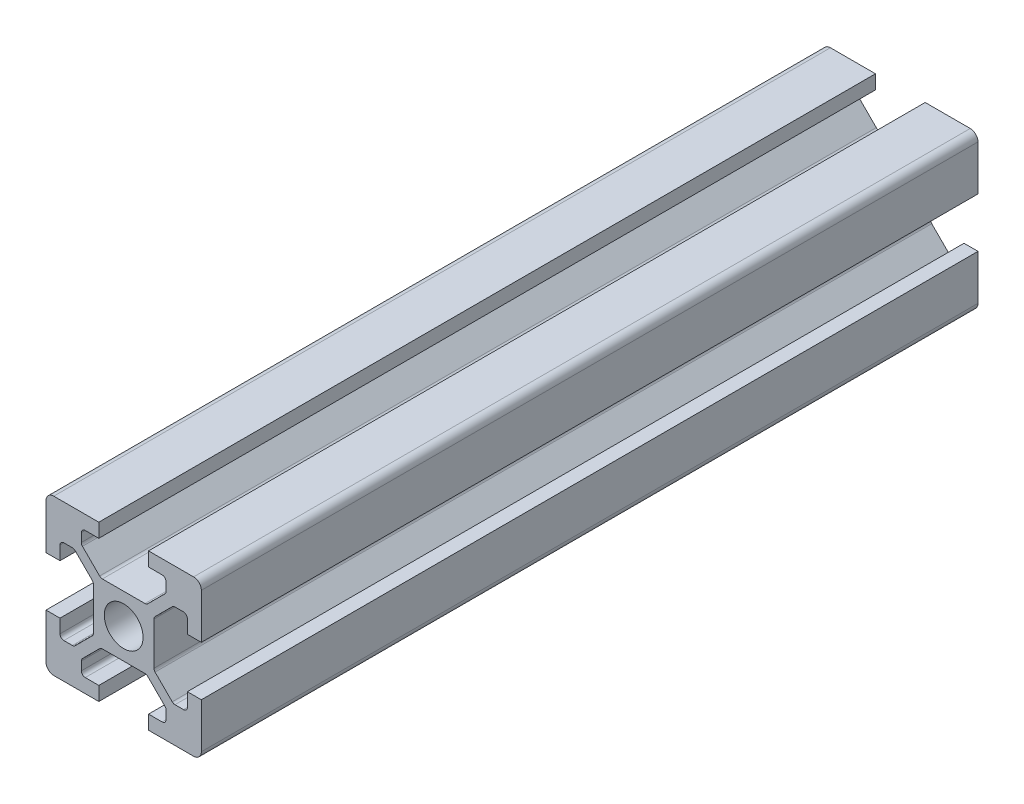
SolidWorks part; units mm, degrees
material "1060 Alloy"
ref_plane "Front Plane" through (0, 0, 0) normal (0, 0, 1) x (1, 0, 0)
ref_plane "Top Plane" through (0, 0, 0) normal (0, 1, 0) x (1, 0, 0)
ref_plane "Right Plane" through (0, 0, 0) normal (1, 0, 0) x (0, 0, -1)
sketch "Sketch1" plane through (0, 0, 0) normal (0, 0, 1) x (1, 0, 0)
  line L0 (20, 0) -> (-8.059, 28.059) construction
  line L1 (0, 0) -> (6.8, 0)
  line L2 (0, 0) -> (0, 6.8)
  line L3 (0, 20) -> (6.8, 20)
  line L4 (20, 0) -> (20, 6.8)
  line L5 (6.8, 20) -> (6.8, 18.2)
  line L6 (20, 20) -> (8.2322, 8.2322) construction
  line L7 (12.95, 6.1) -> (7.05, 6.1)
  line L8 (13.9, 7.05) -> (13.9, 12.95)
  line L9 (12.95, 13.9) -> (7.05, 13.9)
  line L10 (6.1, 7.05) -> (6.1, 12.95)
  line L11 (13.9, 6.1) -> (6.1, 13.9) construction
  line L12 (13.9, 13.9) -> (6.1, 6.1) construction
  line L13 (4.55, 16.4) -> (7.05, 13.9)
  line L14 (13.2, 18.2) -> (13.2, 20)
  line L15 (1.8, 6.8) -> (0, 6.8)
  line L16 (0, 13.2) -> (0, 20)
  line L17 (0, 13.2) -> (1.8, 13.2)
  line L18 (10, 10) -> (10, 13.9) construction
  line L19 (16.4, 4.55) -> (13.9, 7.05)
  line L20 (4.55, 16.4) -> (4.55, 18.2)
  line L21 (4.55, 18.2) -> (6.8, 18.2)
  line L22 (13.2, 18.2) -> (15.45, 18.2)
  line L23 (15.45, 18.2) -> (15.45, 16.4)
  line L24 (15.45, 16.4) -> (12.95, 13.9)
  line L25 (16.4, 4.55) -> (18.2, 4.55)
  line L26 (18.2, 4.55) -> (18.2, 6.8)
  line L27 (20, 6.8) -> (18.2, 6.8)
  line L28 (18.2, 13.2) -> (20, 13.2)
  line L29 (18.2, 13.2) -> (18.2, 15.45)
  line L30 (18.2, 15.45) -> (16.4, 15.45)
  line L31 (16.4, 15.45) -> (13.9, 12.95)
  line L32 (1.8, 4.55) -> (3.6, 4.55)
  line L33 (3.6, 15.45) -> (6.1, 12.95)
  line L34 (3.6, 15.45) -> (1.8, 15.45)
  line L35 (1.8, 15.45) -> (1.8, 13.2)
  line L36 (0, 13.2) -> (1.8, 13.2)
  line L37 (1.8, 6.8) -> (0, 6.8)
  line L38 (3.6, 4.55) -> (6.1, 7.05)
  line L39 (1.8, 6.8) -> (1.8, 4.55)
  line L40 (15.45, 3.6) -> (12.95, 6.1)
  line L41 (4.55, 3.6) -> (7.05, 6.1)
  line L42 (4.55, 1.8) -> (4.55, 3.6)
  line L43 (6.8, 1.8) -> (4.55, 1.8)
  line L44 (6.8, 1.8) -> (6.8, 0)
  line L45 (15.45, 3.6) -> (15.45, 1.8)
  line L46 (15.45, 1.8) -> (13.2, 1.8)
  line L47 (13.2, 0) -> (13.2, 1.8)
  line L48 (13.2, 20) -> (20, 20)
  line L49 (20, 13.2) -> (20, 20)
  line L50 (13.2, 0) -> (20, 0)
  line L51 (6.1, 6.1) -> (-5.5045, -5.5045) construction
  circle A0 centre (10, 10) radius 2.5
  point P25 (10, 16.4)
  point P39 (13.2, 19.1)
  point P46 (0.9, 6.8)
  dimension "D3" = 5
  dimension "D2" = 20
  dimension "D4" = 7.8
  dimension "D5" = 7.8
  dimension "D6" = 6.8
  dimension "D7" = 6.8
  dimension "D8" = 1.8
  dimension "D9" = 10.9
  dimension "D10" = 1.8
  dimension "D11" = 10.9
  dimension "D12" = 20
extrude "Boss-Extrude1" add sketch "Sketch1" along normal blind 100 contours L47 L50 L4 L27 L26 L25 L19 L8 L31 L30 L29 L28 L49 L48 L14 L22 L23 L24 L9 L13 L20 L21 L5 L3 L16 L17 L35 L34 L33 L10 L38 L32 L39 L15 L2 L1 L44 L43 L42 L41 L7 L40 L45 L46 A0
fillet "Fillet1" radius 1 4 edges at (20, 20, 50) (20, 0, 50) (0, 0, 50) (0, 20, 50)
fillet "Fillet2" radius 0.5 6 edges at (4.55, 18.2, 50) (4.55, 16.4, 50) (7.05, 13.9, 50) (15.45, 18.2, 50) (15.45, 16.4, 50) (12.95, 13.9, 50)
fillet "Fillet3" radius 0.5 6 edges at (18.2, 15.45, 50) (16.4, 15.45, 50) (13.9, 12.95, 50) (18.2, 4.55, 50) (13.9, 7.05, 50) (16.4, 4.55, 50)
fillet "Fillet4" radius 0.5 6 edges at (1.8, 15.45, 50) (3.6, 15.45, 50) (6.1, 12.95, 50) (3.6, 4.55, 50) (1.8, 4.55, 50) (6.1, 7.05, 50)
fillet "Fillet5" radius 0.5 6 edges at (7.05, 6.1, 50) (4.55, 3.6, 50) (4.55, 1.8, 50) (15.45, 1.8, 50) (15.45, 3.6, 50) (12.95, 6.1, 50)
